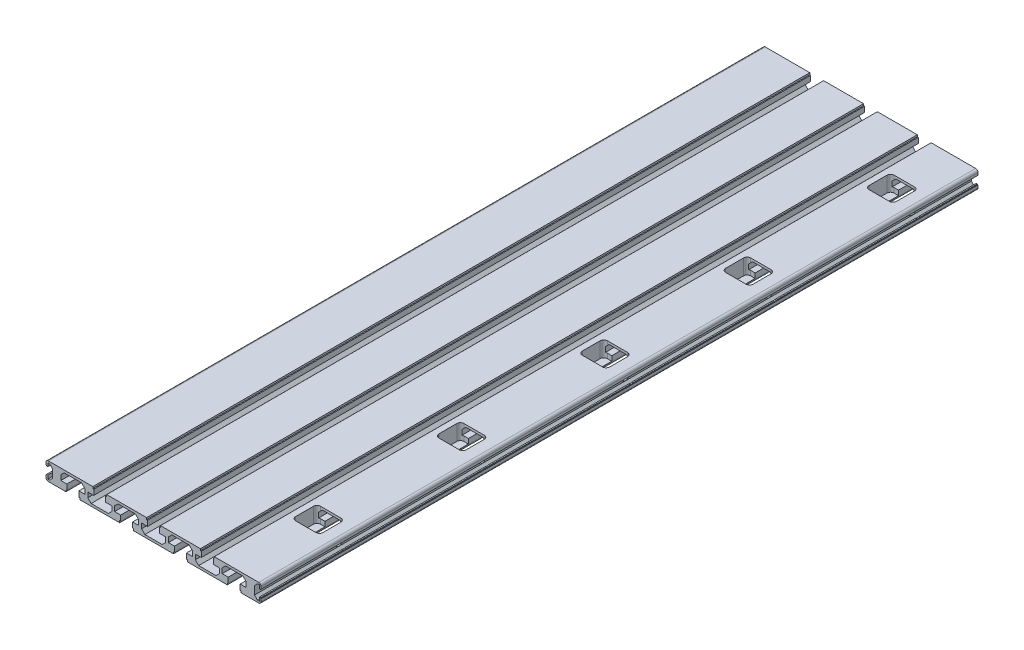
SolidWorks part; units mm, degrees
material "АД31 ГОСТ 4784-97"
ref_plane "Спереди" through (0, 0, 0) normal (0, 0, 1) x (1, 0, 0)
ref_plane "Сверху" through (0, 0, 0) normal (0, 1, 0) x (1, 0, 0)
ref_plane "Справа" through (0, 0, 0) normal (1, 0, 0) x (0, 0, -1)
sketch "Эскиз1" plane through (0, 0, 0) normal (0, 0, 1) x (1, 0, 0)
  line L0 (82.6012, 6.3965) -> (82.6012, 3.3965) construction
  line L1 (82.6012, 3.3965) -> (81.6012, 3.3965) construction
  line L2 (81.6012, 3.3965) -> (81.6012, 2.453) construction
  line L3 (81.6012, -0.6599) -> (81.6012, -1.6035) construction
  line L4 (81.6012, -1.6035) -> (82.6012, -1.6035) construction
  line L5 (82.6012, -1.6035) -> (82.6012, -4.6035) construction
  line L6 (82.6012, -4.6035) -> (78.6012, -4.6035) construction
  line L7 (78.6012, -4.6035) -> (78.6012, -1.6035) construction
  line L8 (78.6012, -1.6035) -> (79.6012, -1.6035) construction
  line L9 (79.6012, -1.6035) -> (79.6012, -0.6599) construction
  line L10 (79.6012, 2.453) -> (79.6012, 3.3965) construction
  line L11 (79.6012, 3.3965) -> (78.6012, 3.3965) construction
  line L12 (78.6012, 3.3965) -> (78.6012, 6.3965) construction
  line L13 (78.6012, 6.3965) -> (82.6012, 6.3965) construction
  line L14 (-83.3988, -4.6035) -> (-83.3988, -1.6035) construction
  line L15 (-83.3988, -1.6035) -> (-82.3988, -1.6035) construction
  line L16 (-82.3988, -1.6035) -> (-82.3988, -0.6599) construction
  line L17 (-82.3988, 2.453) -> (-82.3988, 3.3965) construction
  line L18 (-82.3988, 3.3965) -> (-83.3988, 3.3965) construction
  line L19 (-83.3988, 3.3965) -> (-83.3988, 6.3965) construction
  line L20 (-83.3988, 6.3965) -> (-79.3988, 6.3965) construction
  line L21 (-79.3988, 6.3965) -> (-79.3988, 3.3965) construction
  line L22 (-79.3988, 3.3965) -> (-80.3988, 3.3965) construction
  line L23 (-80.3988, 3.3965) -> (-80.3988, 2.453) construction
  line L24 (-80.3988, -0.6599) -> (-80.3988, -1.6035) construction
  line L25 (-80.3988, -1.6035) -> (-79.3988, -1.6035) construction
  line L26 (-79.3988, -1.6035) -> (-79.3988, -4.6035) construction
  line L27 (-79.3988, -4.6035) -> (-83.3988, -4.6035) construction
  line L28 (-87.4488, -5.1035) -> (-88.8988, -5.1035)
  line L29 (-88.8988, -5.1035) -> (-88.8988, -2.1035)
  line L30 (-88.8988, -2.1035) -> (-89.8988, -2.1035)
  line L31 (-89.8988, -2.1035) -> (-89.8988, -2.6035)
  line L32 (-89.8988, -2.6035) -> (-90.3988, -2.6035)
  line L33 (-90.3988, -2.6035) -> (-90.3988, -4.6035)
  line L34 (-88.3988, -6.6035) -> (-73.6988, -6.6035)
  line L35 (-73.6988, -6.6035) -> (-73.6988, -5.1035)
  line L36 (-73.6988, -5.1035) -> (-72.8988, -5.1035)
  line L37 (-72.8988, -5.1035) -> (-72.8988, -0.6035)
  line L38 (-72.8988, -0.6035) -> (-77.9488, -0.6035)
  line L39 (-77.9488, -0.6035) -> (-77.9488, 3.5965)
  line L40 (-77.9488, 3.5965) -> (-75.1488, 6.3965)
  line L41 (-75.1488, 6.3965) -> (-60.6488, 6.3965)
  line L42 (-60.6488, 6.3965) -> (-57.8488, 3.5965)
  line L43 (-57.8488, 3.5965) -> (-57.8488, -0.6035)
  line L44 (-57.8488, -0.6035) -> (-62.8988, -0.6035)
  line L45 (-62.8988, -0.6035) -> (-62.8988, -5.1035)
  line L46 (-62.8988, -5.1035) -> (-62.0988, -5.1035)
  line L47 (-62.0988, -5.1035) -> (-62.0988, -6.6035)
  line L48 (-62.0988, -6.6035) -> (-28.6988, -6.6035)
  line L49 (-28.6988, -6.6035) -> (-28.6988, -5.1035)
  line L50 (-28.6988, -5.1035) -> (-27.8988, -5.1035)
  line L51 (-27.8988, -5.1035) -> (-27.8988, -0.6035)
  line L52 (-27.8988, -0.6035) -> (-32.9488, -0.6035)
  line L53 (-32.9488, -0.6035) -> (-32.9488, 3.5965)
  line L54 (-32.9488, 3.5965) -> (-30.1488, 6.3965)
  line L55 (-30.1488, 6.3965) -> (-15.6488, 6.3965)
  line L56 (-15.6488, 6.3965) -> (-12.8488, 3.5965)
  line L57 (-12.8488, 3.5965) -> (-12.8488, -0.6035)
  line L58 (-12.8488, -0.6035) -> (-17.8988, -0.6035)
  line L59 (-17.8988, -0.6035) -> (-17.8988, -5.1035)
  line L60 (-17.8988, -5.1035) -> (-17.0988, -5.1035)
  line L61 (-17.0988, -5.1035) -> (-17.0988, -6.6035)
  line L62 (-17.0988, -6.6035) -> (16.3012, -6.6035)
  line L63 (16.3012, -6.6035) -> (16.3012, -5.1035)
  line L64 (16.3012, -5.1035) -> (17.1012, -5.1035)
  line L65 (17.1012, -5.1035) -> (17.1012, -0.6035)
  line L66 (17.1012, -0.6035) -> (12.0512, -0.6035)
  line L67 (12.0512, -0.6035) -> (12.0512, 3.5965)
  line L68 (12.0512, 3.5965) -> (14.8512, 6.3965)
  line L69 (14.8512, 6.3965) -> (29.3512, 6.3965)
  line L70 (29.3512, 6.3965) -> (32.1512, 3.5965)
  line L71 (32.1512, 3.5965) -> (32.1512, -0.6035)
  line L72 (32.1512, -0.6035) -> (27.1012, -0.6035)
  line L73 (27.1012, -0.6035) -> (27.1012, -5.1035)
  line L74 (27.1012, -5.1035) -> (27.9012, -5.1035)
  line L75 (27.9012, -5.1035) -> (27.9012, -6.6035)
  line L76 (27.9012, -6.6035) -> (61.3012, -6.6035)
  line L77 (61.3012, -6.6035) -> (61.3012, -5.1035)
  line L78 (61.3012, -5.1035) -> (62.1012, -5.1035)
  line L79 (62.1012, -5.1035) -> (62.1012, -0.6035)
  line L80 (62.1012, -0.6035) -> (57.0512, -0.6035)
  line L81 (57.0512, -0.6035) -> (57.0512, 3.5965)
  line L82 (57.0512, 3.5965) -> (59.8512, 6.3965)
  line L83 (59.8512, 6.3965) -> (74.3512, 6.3965)
  line L84 (74.3512, 6.3965) -> (77.1512, 3.5965)
  line L85 (77.1512, 3.5965) -> (77.1512, -0.6035)
  line L86 (77.1512, -0.6035) -> (72.1012, -0.6035)
  line L87 (72.1012, -0.6035) -> (72.1012, -5.1035)
  line L88 (72.1012, -5.1035) -> (72.9012, -5.1035)
  line L89 (72.9012, -5.1035) -> (72.9012, -6.6035)
  line L90 (72.9012, -6.6035) -> (87.6012, -6.6035)
  line L91 (89.6012, -4.6035) -> (89.6012, -2.6035)
  line L92 (89.6012, -2.6035) -> (89.1012, -2.6035)
  line L93 (89.1012, -2.6035) -> (89.1012, -2.1035)
  line L94 (89.1012, -2.1035) -> (88.1012, -2.1035)
  line L95 (88.1012, -2.1035) -> (88.1012, -5.1035)
  line L96 (88.1012, -5.1035) -> (86.6512, -5.1035)
  line L97 (86.6512, -5.1035) -> (84.1012, -2.5535)
  line L98 (84.1012, -2.5535) -> (84.1012, 4.3465)
  line L99 (84.1012, 4.3465) -> (86.6512, 6.8965)
  line L100 (86.6512, 6.8965) -> (88.1012, 6.8965)
  line L101 (88.1012, 6.8965) -> (88.1012, 3.8965)
  line L102 (88.1012, 3.8965) -> (89.1012, 3.8965)
  line L103 (89.1012, 3.8965) -> (89.1012, 4.3965)
  line L104 (89.1012, 4.3965) -> (89.6012, 4.3965)
  line L105 (89.6012, 4.3965) -> (89.6012, 6.3965)
  line L106 (87.6012, 8.3965) -> (50.4012, 8.3965)
  line L107 (50.4012, 8.3965) -> (50.4012, 6.8965)
  line L108 (50.4012, 6.8965) -> (49.6012, 6.8965)
  line L109 (49.6012, 6.8965) -> (49.6012, 2.3965)
  line L110 (49.6012, 2.3965) -> (54.6512, 2.3965)
  line L111 (54.6512, 2.3965) -> (54.6512, -1.8035)
  line L112 (54.6512, -1.8035) -> (51.8512, -4.6035)
  line L113 (51.8512, -4.6035) -> (37.3512, -4.6035)
  line L114 (37.3512, -4.6035) -> (34.5512, -1.8035)
  line L115 (34.5512, -1.8035) -> (34.5512, 2.3965)
  line L116 (34.5512, 2.3965) -> (39.6012, 2.3965)
  line L117 (39.6012, 2.3965) -> (39.6012, 6.8965)
  line L118 (39.6012, 6.8965) -> (38.8012, 6.8965)
  line L119 (38.8012, 6.8965) -> (38.8012, 8.3965)
  line L120 (38.8012, 8.3965) -> (5.4012, 8.3965)
  line L121 (5.4012, 8.3965) -> (5.4012, 6.8965)
  line L122 (5.4012, 6.8965) -> (4.6012, 6.8965)
  line L123 (4.6012, 6.8965) -> (4.6012, 2.3965)
  line L124 (4.6012, 2.3965) -> (9.6512, 2.3965)
  line L125 (9.6512, 2.3965) -> (9.6512, -1.8035)
  line L126 (9.6512, -1.8035) -> (6.8512, -4.6035)
  line L127 (6.8512, -4.6035) -> (-7.6488, -4.6035)
  line L128 (-7.6488, -4.6035) -> (-10.4488, -1.8035)
  line L129 (-10.4488, -1.8035) -> (-10.4488, 2.3965)
  line L130 (-10.4488, 2.3965) -> (-5.3988, 2.3965)
  line L131 (-5.3988, 2.3965) -> (-5.3988, 6.8965)
  line L132 (-5.3988, 6.8965) -> (-6.1988, 6.8965)
  line L133 (-6.1988, 6.8965) -> (-6.1988, 8.3965)
  line L134 (-6.1988, 8.3965) -> (-39.5988, 8.3965)
  line L135 (-39.5988, 8.3965) -> (-39.5988, 6.8965)
  line L136 (-39.5988, 6.8965) -> (-40.3988, 6.8965)
  line L137 (-40.3988, 6.8965) -> (-40.3988, 2.3965)
  line L138 (-40.3988, 2.3965) -> (-35.3488, 2.3965)
  line L139 (-35.3488, 2.3965) -> (-35.3488, -1.8035)
  line L140 (-35.3488, -1.8035) -> (-38.1488, -4.6035)
  line L141 (-38.1488, -4.6035) -> (-52.6488, -4.6035)
  line L142 (-52.6488, -4.6035) -> (-55.4488, -1.8035)
  line L143 (-55.4488, -1.8035) -> (-55.4488, 2.3965)
  line L144 (-55.4488, 2.3965) -> (-50.3988, 2.3965)
  line L145 (-50.3988, 2.3965) -> (-50.3988, 6.8965)
  line L146 (-50.3988, 6.8965) -> (-51.1988, 6.8965)
  line L147 (-51.1988, 6.8965) -> (-51.1988, 8.3965)
  line L148 (-51.1988, 8.3965) -> (-88.3988, 8.3965)
  line L149 (-90.3988, 6.3965) -> (-90.3988, 4.3965)
  line L150 (-90.3988, 4.3965) -> (-89.8988, 4.3965)
  line L151 (-89.8988, 4.3965) -> (-89.8988, 3.8965)
  line L152 (-89.8988, 3.8965) -> (-88.8988, 3.8965)
  line L153 (-88.8988, 3.8965) -> (-88.8988, 6.8965)
  line L154 (-88.8988, 6.8965) -> (-87.4488, 6.8965)
  line L155 (-87.4488, 6.8965) -> (-84.8988, 4.3465)
  line L156 (-84.8988, 4.3465) -> (-84.8988, -2.5535)
  line L157 (-84.8988, -2.5535) -> (-87.4488, -5.1035)
  arc A0 (81.6012, 2.453) -> (81.6012, -0.6599) centre (80.6012, 0.8965) cw construction
  arc A1 (79.6012, -0.6599) -> (79.6012, 2.453) centre (80.6012, 0.8965) cw construction
  arc A2 (-82.3988, -0.6599) -> (-82.3988, 2.453) centre (-81.3988, 0.8965) cw construction
  arc A3 (-80.3988, 2.453) -> (-80.3988, -0.6599) centre (-81.3988, 0.8965) cw construction
  arc A4 (-90.3988, -4.6035) -> (-88.3988, -6.6035) centre (-88.3988, -4.6035) ccw
  arc A5 (87.6012, -6.6035) -> (89.6012, -4.6035) centre (87.6012, -4.6035) ccw
  arc A6 (89.6012, 6.3965) -> (87.6012, 8.3965) centre (87.6012, 6.3965) ccw
  arc A7 (-88.3988, 8.3965) -> (-90.3988, 6.3965) centre (-88.3988, 6.3965) ccw
extrude "Бобышка-Вытянуть1" add sketch "Эскиз1" along normal blind 600
sketch "Эскиз2" [suppressed] plane through (0, 8.3965, 0) normal (0, 1, 0) x (1, 0, 0)
  line L0 (-67.8988, 41.3183) -> (-67.8988, -223.5734) construction
  line L1 (0, 26.2034) -> (0, -217.3135) construction
  line L2 (67.1012, 26.2034) -> (67.1012, -223.5734) construction
  line L3 (89.6012, -200) -> (89.6012, 0) construction
  line L4 (-90.3988, -200) -> (-90.3988, 0) construction
  dimension "D1" = 22.5
  dimension "D2" = 22.5
hole_wizard "Зенковка для винта с потайной головкой и внутренним шестигранником M41" positions "Трехмерный эскиз1" profile "Эскиз3" countersink size "M4" standard "ISO"
sketch3d "Трехмерный эскиз1" [suppressed]
  line L0 (-67.8988, 8.3965, -41.3183) -> (-67.8988, 8.3965, 223.5734) construction
  line L1 (-51.1988, 8.3965, 0) -> (-88.3988, 8.3965, 0) construction
  point P0 (-67.8988, 8.3965, 15)
  point P4 (-67.8988, 8.3965, 40)
  point P6 (-67.8988, 8.3965, 65)
  point P8 (-67.8988, 8.3965, 95)
  point P10 (-67.8988, 8.3965, 120)
  point P12 (-67.8988, 8.3965, 145)
  dimension "D1" = 15
  dimension "D2" = 25
  dimension "D3" = 25
  dimension "D4" = 25
  dimension "D5" = 25
  dimension "D6" = 30
sketch "Эскиз3" plane through (-67.8988, 8.3965, 15) normal (1, 0, 0) x (0, 0, 1)
  line L0 (0, 0) -> (0, 26.25)
  line L1 (0, 26.25) -> (2.4, 26.25)
  line L2 (2.4, 26.25) -> (2.4, 2.08)
  line L3 (2.4, 2.08) -> (4.48, 0)
  line L5 (4.48, 0) -> (0, 0)
  line L6 (-2.4, 2.08) -> (-4.48, 0) construction
  line L10 (0, 26.25) -> (-2.4, 26.25) construction
  line L11 (0, -6.35) -> (0, 107.95) construction
  dimension "Диаметр отверстия" = 4.8
  dimension "Глубина отверстия" = 26.25
  dimension "Диаметр передней зенковки" = 8.96
  dimension "Угол передней зенковки" = 90
  dimension "Угол заточки сверла" = 180
ref_plane "Плоскость1" through (-0.3988, 0, 0) normal (-1, 0, 0) x (0, 0, 1)
ref_plane "Плоскость2" through (0, 0, 300) normal (0, 0, 1) x (1, 0, 0)
move or copy body "Тело-Переместить/Копировать1" bodies to move or copy 103
sketch "Эскиз4" plane through (0, 8.3965, 0) normal (0, 1, 0) x (1, 0, 0)
  line L0 (75.4012, 81) -> (58.4012, 81)
  line L5 (89.6012, 600) -> (89.6012, 0) construction
  line L8 (75.4012, 60) -> (58.4012, 60)
  line L9 (78.4012, 78) -> (78.4012, 63)
  line L10 (55.4012, 78) -> (55.4012, 63)
  line L12 (87.6012, 0) -> (50.4012, 0) construction
  arc A6 (75.4012, 60) -> (78.4012, 63) centre (75.4012, 63) ccw
  arc A7 (58.4012, 60) -> (55.4012, 63) centre (58.4012, 63) cw
  arc A8 (55.4012, 78) -> (58.4012, 81) centre (58.4012, 78) cw
  arc A9 (78.4012, 78) -> (75.4012, 81) centre (75.4012, 78) ccw
  dimension "D3" = 60
  dimension "D2" = 3
  dimension "D1" = 23
  dimension "D4" = 11.2
  dimension "D7" = 17
extrude "Вырез-Вытянуть1" cut sketch "Эскиз4" against normal blind 13
sketch "Эскиз5" plane through (77.1512, 0, 0) normal (-1, 0, 0) x (0, 0, 1)
  line L2 (-63, -4.6035) -> (-63, 8.3965) construction
  circle A0 centre (-70.5, 0.8965) radius 3.25
  dimension "D1" = 7.5
extrude "Вырез-Вытянуть2" cut sketch "Эскиз5" against normal through all
pattern_linear "Линейный массив1" count 5 spacing 120 along (0, 0, -1) of "Вырез-Вытянуть1", "Вырез-Вытянуть2"
